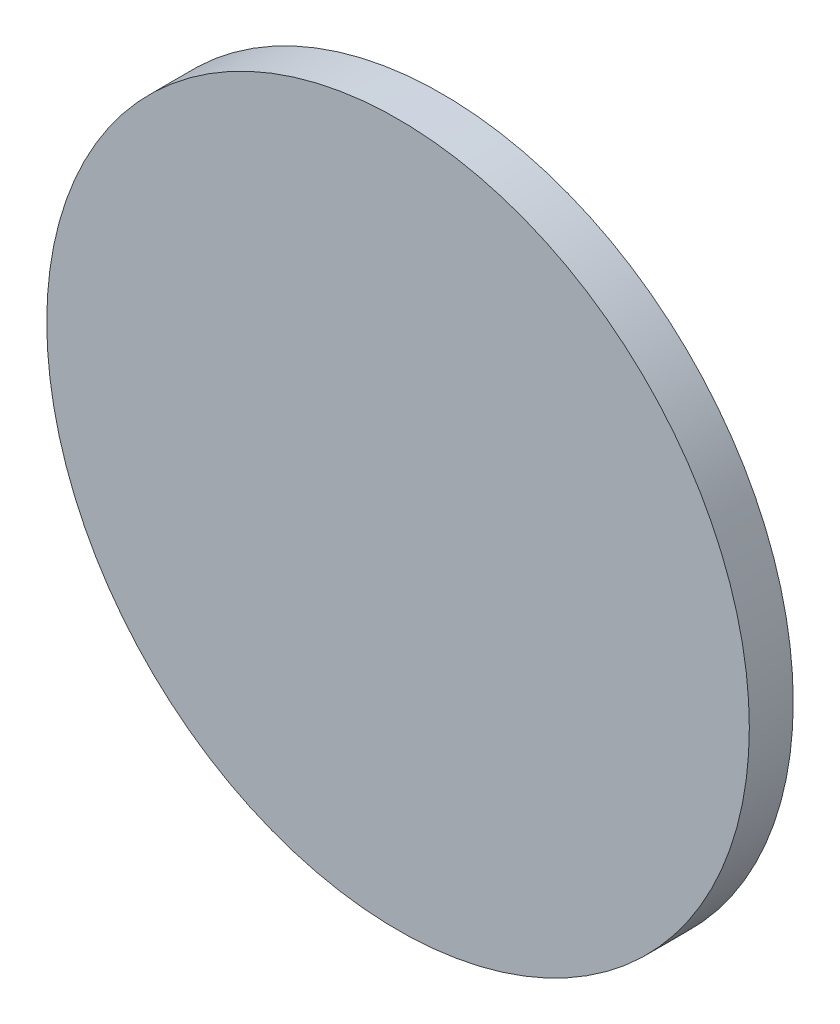
SolidWorks part; units mm, degrees
material "Acrylic (Medium-high impact)"
ref_plane "Front Plane" through (0, 0, 0) normal (0, 0, 1) x (1, 0, 0)
ref_plane "Top Plane" through (0, 0, 0) normal (0, 1, 0) x (1, 0, 0)
ref_plane "Right Plane" through (0, 0, 0) normal (1, 0, 0) x (0, 0, -1)
sketch "Sketch2" plane through (0, 0, 0) normal (0, 0, 1) x (1, 0, 0)
  circle A1 centre (0, 0) radius 25.4
  circle A2 centre (0, 0) radius 25.4
  dimension "D1" = 0
extrude "Boss-Extrude1" add sketch "Sketch2" along normal blind 3.175
